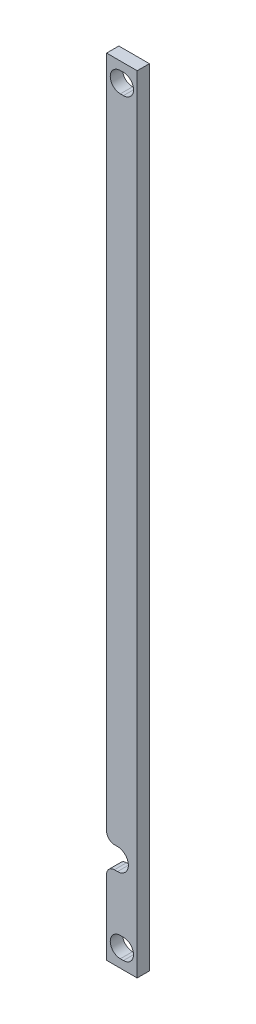
SolidWorks part; units mm, degrees
ref_plane "Front Plane" through (0, 0, 0) normal (0, 0, 1) x (1, 0, 0)
ref_plane "Top Plane" through (0, 0, 0) normal (0, 1, 0) x (1, 0, 0)
ref_plane "Right Plane" through (0, 0, 0) normal (1, 0, 0) x (0, 0, -1)
sketch "Sketch1" plane through (0, 0, 0) normal (0, 0, 1) x (1, 0, 0)
  line L0 (0, 64.25) -> (0, -64.25) construction
  line L1 (-2.5, 64.25) -> (2.5, 64.25)
  line L2 (-2.5, 64.25) -> (-2.5, -64.25)
  line L3 (-2.5, -64.25) -> (2.5, -64.25)
  line L4 (2.5, 64.25) -> (2.5, -64.25)
  line L5 (-2.5, 64.25) -> (2.5, -64.25) construction
  line L6 (-2.5, -64.25) -> (2.5, 64.25) construction
  line L7 (-2.5, 61.25) -> (2.5, 61.25) construction
  line L8 (-2.5, -61.25) -> (2.5, -61.25) construction
  line L9 (-0.254, -61.25) -> (0.254, -61.25) construction
  line L11 (-0.254, -59.6) -> (0.254, -59.6)
  line L12 (-0.254, -62.9) -> (0.254, -62.9)
  line L13 (-0.254, 61.25) -> (0.254, 61.25) construction
  line L14 (-0.254, 62.9) -> (0.254, 62.9)
  line L15 (-0.254, 59.6) -> (0.254, 59.6)
  arc A0 (-0.254, -59.6) -> (-0.254, -62.9) centre (-0.254, -61.25) ccw
  arc A1 (0.254, -62.9) -> (0.254, -59.6) centre (0.254, -61.25) ccw
  arc A2 (-0.254, 62.9) -> (-0.254, 59.6) centre (-0.254, 61.25) ccw
  arc A3 (0.254, 59.6) -> (0.254, 62.9) centre (0.254, 61.25) ccw
  point P0 (0, 0)
  point P18 (0, -61.25)
  point P24 (0, 61.25)
  dimension "D6" = 1.65
  dimension "D7" = 1.65
  dimension "D3" = 0.508
  dimension "D8" = 0.508
  dimension "D1" = 128.5
  dimension "D2" = 5
  dimension "D4" = 3
  dimension "D5" = 3
extrude "Boss-Extrude1" add sketch "Sketch1" along normal blind 2
sketch "Sketch2" plane through (0, 0, 2) normal (0, 0, 1) x (1, 0, 0)
  line L0 (-2.5, 64.25) -> (-2.5, -64.25) construction
  line L1 (-2.5, -64.25) -> (2.5, -64.25) construction
  line L2 (-0.722, -47.232) -> (-2.5, -47.232)
  line L3 (-2.5, -47.232) -> (-2.5, -50.788)
  line L4 (-2.5, -50.788) -> (-0.722, -50.788)
  arc A0 (-0.722, -50.788) -> (-0.722, -47.232) centre (-0.722, -49.01) ccw
  dimension "D1" = 3.556
  dimension "D2" = 15.24
extrude "Cut-Extrude1" cut sketch "Sketch2" against normal blind 2.54
fillet "Fillet1" radius 1.27 2 edges at (-2.5, -50.788, 1) (-2.5, -47.232, 1)
